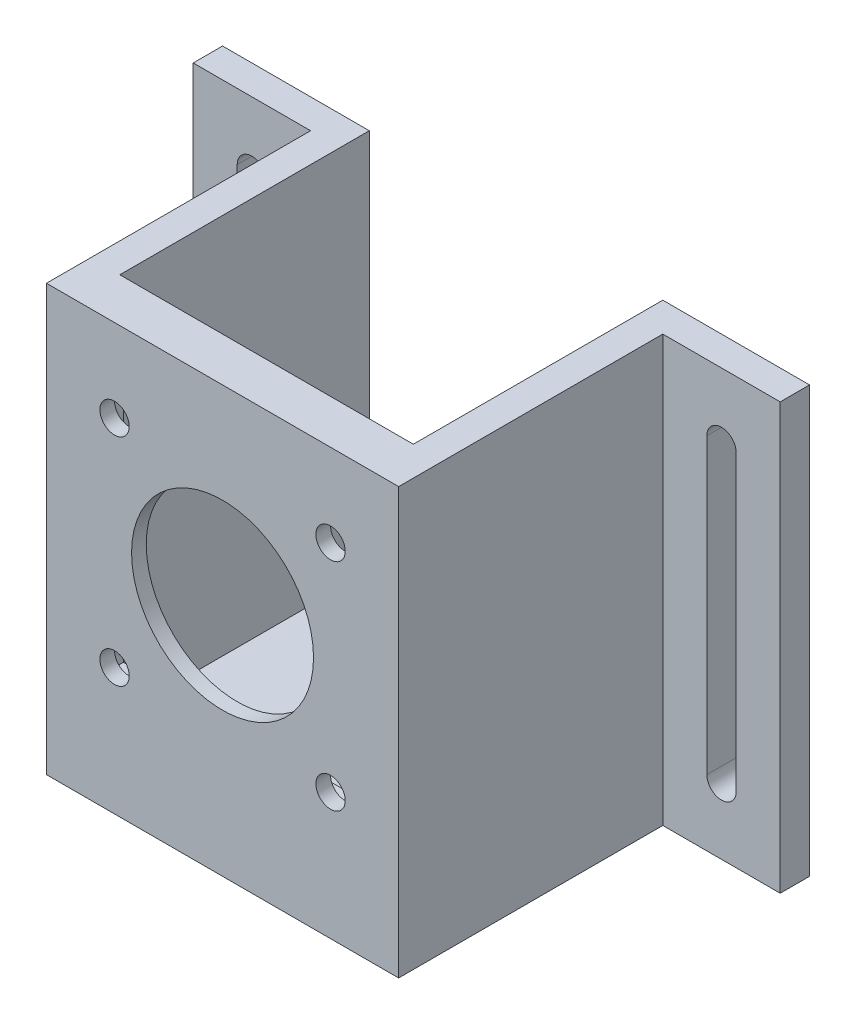
SolidWorks part; units mm, degrees
ref_plane "Front Plane" through (0, 0, 0) normal (0, 0, 1) x (1, 0, 0)
ref_plane "Top Plane" through (0, 0, 0) normal (0, 1, 0) x (1, 0, 0)
ref_plane "Right Plane" through (0, 0, 0) normal (1, 0, 0) x (0, 0, -1)
sketch "Sketch2" plane through (0, 0, 0) normal (0, 1, 0) x (1, 0, 0)
  line L1 (0, 0) -> (76.2, 0)
  line L2 (0, 0) -> (0, 63.5)
  line L3 (0, 63.5) -> (76.2, 63.5)
  line L4 (76.2, 0) -> (76.2, 63.5)
  dimension "D1" = 63.5
  dimension "D2" = 76.2
extrude "Boss-Extrude1" add sketch "Sketch2" along normal blind 9.525
sketch "Sketch3" plane through (0, 9.525, 0) normal (0, 1, 0) x (1, 0, 0)
  line L0 (76.2, 0) -> (76.2, 63.5) construction
  line L1 (0, 0) -> (76.2, 0)
  line L2 (0, 0) -> (0, 9.525)
  line L3 (0, 9.525) -> (76.2, 9.525)
  line L4 (76.2, 0) -> (76.2, 9.525)
  dimension "D1" = 9.525
extrude "Boss-Extrude2" add sketch "Sketch3" along normal blind 82.55
sketch "Sketch7" plane through (0, 0, -9.525) normal (0, 0, -1) x (-1, 0, 0)
  line L0 (-38.1, 92.075) -> (-38.1, 9.525) construction
  line L1 (-76.2, 92.075) -> (0, 92.075) construction
  line L2 (-76.2, 9.525) -> (0, 9.525) construction
  line L3 (-38.1, 50.8) -> (-24.0683, 50.8) construction
  circle A0 centre (-38.1, 50.8) radius 19.685
  circle A2 centre (-61.468, 74.168) radius 3.175
  circle A3 centre (-14.732, 74.168) radius 3.175
  circle A6 centre (-14.732, 27.432) radius 3.175
  circle A7 centre (-61.468, 27.432) radius 3.175
  dimension "D1" = 23.368
  dimension "D2" = 23.368
  dimension "D3" = 23.368
  dimension "D4" = 23.368
extrude "Cut-Extrude1" cut sketch "Sketch7" against normal through all
sketch "Sketch11" plane through (0, 0, -9.525) normal (0, 0, -1) x (-1, 0, 0)
  line L1 (-69.0607, 81.7423) -> (-7.1393, 81.7423)
  line L2 (-69.0607, 81.7423) -> (-69.0607, 19.8577)
  line L3 (-69.0607, 19.8577) -> (-7.1393, 19.8577)
  line L4 (-7.1393, 81.7423) -> (-7.1393, 19.8577)
  line L5 (-69.0607, 81.7423) -> (-7.1393, 19.8577) construction
  line L6 (-69.0607, 19.8577) -> (-7.1393, 81.7423) construction
  point P0 (-38.1, 50.8)
extrude "Cut-Extrude4" cut sketch "Sketch11" against normal blind 6.35
sketch "Sketch12" plane through (0, 9.525, 0) normal (0, 1, 0) x (1, 0, 0)
  line L0 (76.2, 63.5) -> (0, 63.5) construction
  line L1 (76.2, 9.525) -> (69.85, 9.525)
  line L2 (76.2, 9.525) -> (76.2, 63.5)
  line L3 (76.2, 63.5) -> (69.85, 63.5)
  line L4 (69.85, 9.525) -> (69.85, 63.5)
  line L6 (0, 9.525) -> (6.35, 9.525)
  line L7 (0, 9.525) -> (0, 63.5)
  line L8 (0, 63.5) -> (6.35, 63.5)
  line L9 (6.35, 9.525) -> (6.35, 63.5)
  dimension "D1" = 6.35
  dimension "D2" = 6.35
extrude "Boss-Extrude3" add sketch "Sketch12" along normal up to surface (82.55 mm away) up to face at (38.1, 92.075, -4.7625)
sketch "Sketch14" plane through (0, 0, 0) normal (-1, 0, 0) x (0, 0, 1)
  line L0 (-63.5, 0) -> (0, 0) construction
  line L1 (-63.5, 92.075) -> (-57.15, 92.075)
  line L2 (-63.5, 92.075) -> (-63.5, 0)
  line L3 (-63.5, 0) -> (-57.15, 0)
  line L4 (-57.15, 92.075) -> (-57.15, 0)
  dimension "D1" = 6.35
extrude "Boss-Extrude5" add sketch "Sketch14" along normal blind 25.4
sketch "Sketch15" plane through (76.2, 0, 0) normal (1, 0, 0) x (0, 0, -1)
  line L0 (0, 92.075) -> (63.5, 92.075) construction
  line L1 (63.5, 0) -> (57.15, 0)
  line L2 (63.5, 0) -> (63.5, 92.075)
  line L3 (63.5, 92.075) -> (57.15, 92.075)
  line L4 (57.15, 0) -> (57.15, 92.075)
  dimension "D1" = 6.35
extrude "Boss-Extrude6" add sketch "Sketch15" along normal blind 25.4
sketch "Sketch16" plane through (0, 0, -57.15) normal (0, 0, 1) x (1, 0, 0)
  line L0 (88.9, 0) -> (88.9, 92.075) construction
  line L1 (101.6, 0) -> (76.2, 0) construction
  line L2 (101.6, 92.075) -> (76.2, 92.075) construction
  line L6 (101.6, 46.0375) -> (-25.4, 46.0375) construction
  line L7 (101.6, 92.075) -> (101.6, 0) construction
  line L8 (-25.4, 0) -> (-25.4, 92.075) construction
  line L9 (-15.875, 77.7875) -> (-15.875, 14.2875)
  line L10 (-9.525, 77.7875) -> (-9.525, 14.2875)
  line L11 (85.725, 14.2875) -> (85.725, 77.7875)
  line L12 (92.075, 77.7875) -> (92.075, 14.2875)
  arc A0 (92.075, 77.7875) -> (85.725, 77.7875) centre (88.9, 77.7875) ccw
  arc A1 (92.075, 14.2875) -> (85.725, 14.2875) centre (88.9, 14.2875) cw
  arc A2 (-9.525, 77.7875) -> (-15.875, 77.7875) centre (-12.7, 77.7875) ccw
  arc A3 (-15.875, 14.2875) -> (-9.525, 14.2875) centre (-12.7, 14.2875) ccw
  point P20 (88.9, 46.0375)
  dimension "D1" = 31.75
extrude "Cut-Extrude5" cut sketch "Sketch16" against normal through all
